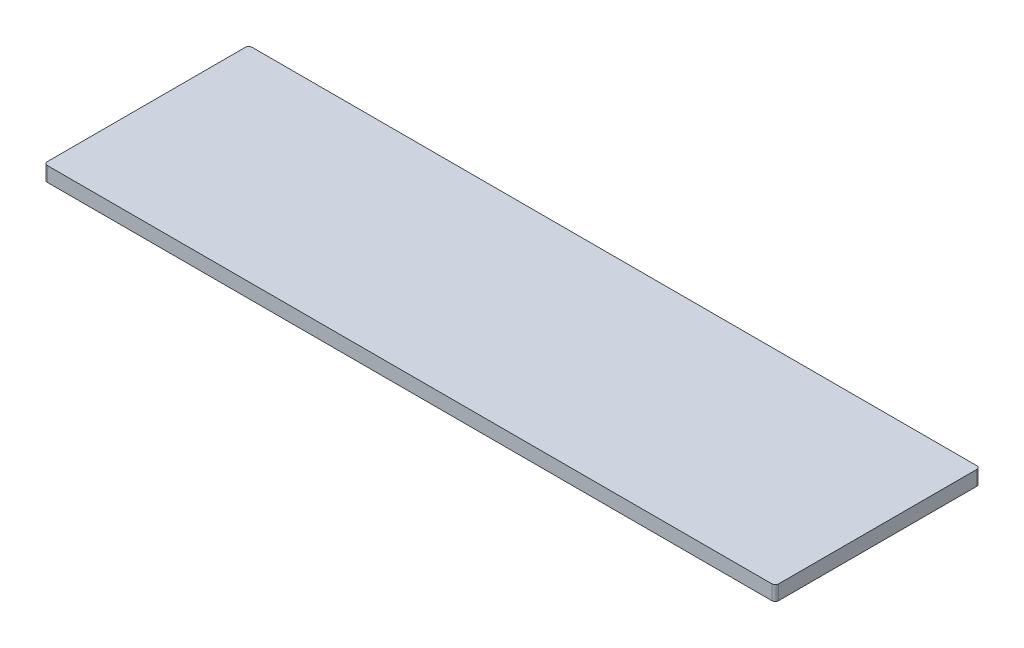
SolidWorks part; units mm, degrees
ref_plane "Front Plane" through (0, 0, 0) normal (0, 0, 1) x (1, 0, 0)
ref_plane "Top Plane" through (0, 0, 0) normal (0, 1, 0) x (1, 0, 0)
ref_plane "Right Plane" through (0, 0, 0) normal (1, 0, 0) x (0, 0, -1)
sketch "Sketch1" plane through (0, 0, 0) normal (0, 1, 0) x (1, 0, 0)
  line L1 (-317.5, -88.9) -> (317.5, -88.9)
  line L2 (-317.5, -88.9) -> (-317.5, 88.9)
  line L3 (-317.5, 88.9) -> (317.5, 88.9)
  line L4 (317.5, -88.9) -> (317.5, 88.9)
  line L5 (-317.5, -88.9) -> (317.5, 88.9) construction
  line L6 (-317.5, 88.9) -> (317.5, -88.9) construction
  point P0 (0, 0)
  dimension "D1" = 635
  dimension "D2" = 177.8
extrude "Boss-Extrude1" add sketch "Sketch1" along normal blind 12.7
fillet "Fillet1" radius 3 4 edges at (-317.5, 6.35, 88.9) (-317.5, 6.35, -88.9) (317.5, 6.35, -88.9) (317.5, 6.35, 88.9)
